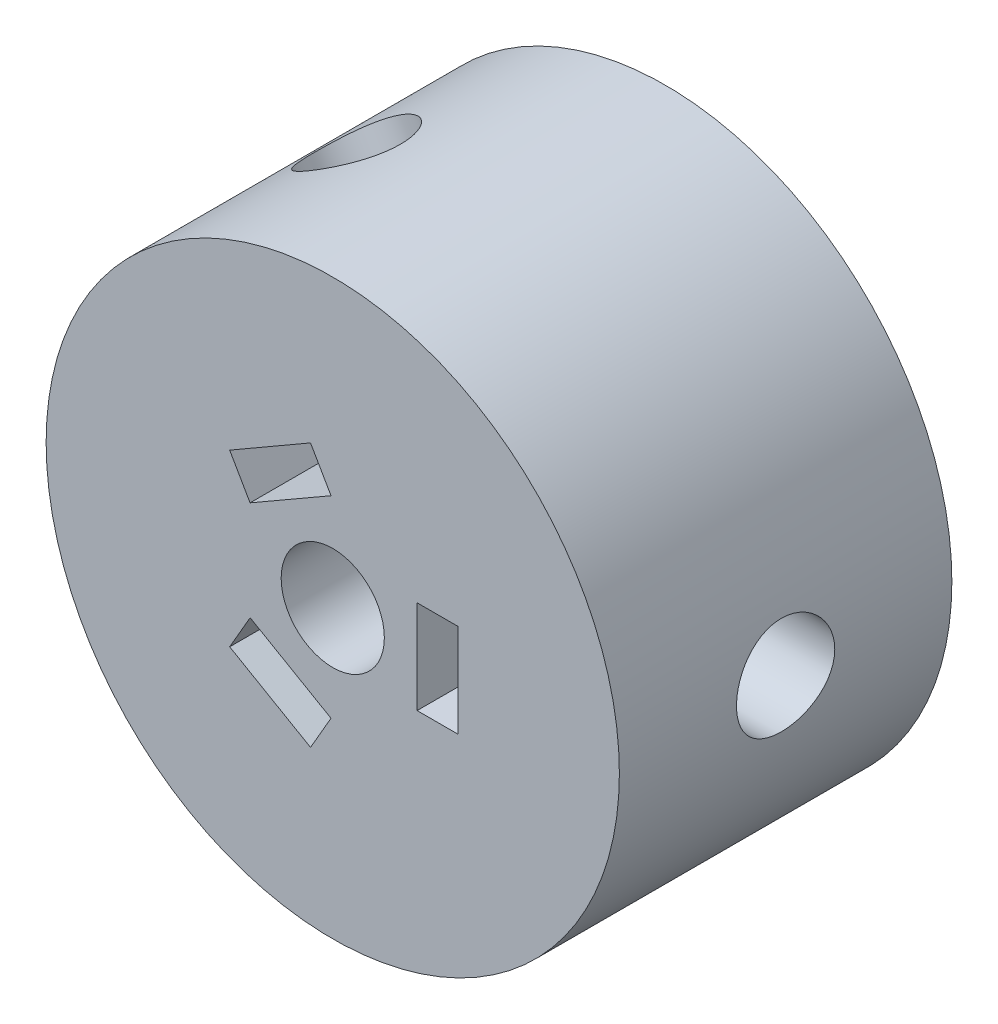
SolidWorks part; units mm, degrees
ref_plane "Front" through (0, 0, 0) normal (0, 0, 1) x (1, 0, 0)
ref_plane "Top" through (0, 0, 0) normal (0, 1, 0) x (1, 0, 0)
ref_plane "Right" through (0, 0, 0) normal (1, 0, 0) x (0, 0, -1)
sketch "Sketch1" plane through (0, 0, 0) normal (0, 0, 1) x (1, 0, 0)
  circle A0 centre (0, 0) radius 17.5
  circle A1 centre (0, 0) radius 3.15
  dimension "D1" = 35
  dimension "D2" = 6.3
extrude "Boss-Extrude1" add sketch "Sketch1" along normal blind 40.3
sketch "Sketch2" plane through (0, 0, 40.3) normal (0, 0, 1) x (1, 0, 0)
  line L3 (7.65, 0) -> (7.65, 2.85)
  line L5 (7.65, 0) -> (7.65, -2.85)
  line L7 (7.65, 2.85) -> (5.15, 2.85)
  line L8 (5.15, 2.85) -> (5.15, -2.85)
  line L9 (5.15, -2.85) -> (7.65, -2.85)
  line L16 (-3.825, -6.6251) -> (-1.3568, -8.0501)
  line L17 (-3.825, -6.6251) -> (-6.2932, -5.2001)
  line L18 (-1.3568, -8.0501) -> (-0.1068, -5.885)
  line L19 (-0.1068, -5.885) -> (-5.0432, -3.035)
  line L20 (-5.0432, -3.035) -> (-6.2932, -5.2001)
  line L21 (-3.825, 6.6251) -> (-6.2932, 5.2001)
  line L22 (-3.825, 6.6251) -> (-1.3568, 8.0501)
  line L23 (-1.3568, 8.0501) -> (-0.1054, 5.8826)
  line L24 (-0.1054, 5.8826) -> (-5.0482, 3.0353)
  line L25 (-5.0482, 3.0353) -> (-6.2932, 5.2001)
  dimension "D5" = 2.85
  dimension "D6" = 2.85
  dimension "D7" = 2.85
  dimension "D8" = 2.85
  dimension "D9" = 2.5
  dimension "D10" = 5.7
  dimension "D11" = 2.85
extrude "Cut-Extrude1" cut sketch "Sketch2" against normal blind 23 contours L9 L5 L3 L7 L8 | L25 L21 L22 L23 L24 | L20 L17 L16 L18 L19
ref_plane "Plane1" through (-8.75, -15.1554, 0) normal (-0.5, -0.866, 0) x (0, 0, -1)
sketch "Sketch8" plane through (-8.75, -15.1554, 0) normal (-0.5, -0.866, 0) x (0, 0, -1)
  circle A0 centre (-20.15, 0) radius 1.65
  dimension "D1" = 3.3
extrude "Cut-Extrude4" cut sketch "Sketch8" against normal up to next
sketch "Sketch10" plane through (-8.75, -15.1554, 0) normal (-0.5, -0.866, 0) x (0, 0, -1)
  circle A0 centre (-20.15, 0) radius 1.65
extrude "Cut-Extrude5" cut sketch "Sketch10" against normal up to next
sketch "Sketch12" plane through (-8.75, -15.1554, 0) normal (-0.5, -0.866, 0) x (0, 0, -1)
  circle A0 centre (-20.15, 0) radius 3
  dimension "D1" = 6
extrude "Cut-Extrude6" cut sketch "Sketch12" against normal blind 5.35
ref_plane "Plane2" through (-8.75, 15.1554, 0) normal (-0.5, 0.866, 0) x (0, 0, -1)
sketch "Sketch15" plane through (-8.75, 15.1554, 0) normal (-0.5, 0.866, 0) x (0, 0, -1)
  circle A0 centre (-20.15, 0) radius 3
extrude "Cut-Extrude8" cut sketch "Sketch15" against normal blind 5.35
sketch "Sketch17" plane through (-8.75, 15.1554, 0) normal (-0.5, 0.866, 0) x (0, 0, -1)
  circle A0 centre (-20.15, 0) radius 1.65
  dimension "D1" = 3.3
extrude "Cut-Extrude9" cut sketch "Sketch17" against normal up to next
sketch "Sketch18" plane through (-8.75, 15.1554, 0) normal (-0.5, 0.866, 0) x (0, 0, -1)
  circle A0 centre (-20.15, 0) radius 1.65
extrude "Cut-Extrude10" cut sketch "Sketch18" against normal up to next
ref_plane "Plane3" through (17.5, 0, 0) normal (1, 0, 0) x (0, 0, -1)
sketch "Sketch19" plane through (17.5, 0, 0) normal (1, 0, 0) x (0, 0, -1)
  circle A0 centre (-20.15, 0) radius 3
extrude "Cut-Extrude11" cut sketch "Sketch19" against normal blind 5.35 contours A0
sketch "Sketch20" plane through (17.5, 0, 0) normal (1, 0, 0) x (0, 0, -1)
  circle A0 centre (-20.15, 0) radius 1.65
  dimension "D1" = 3.3
extrude "Cut-Extrude12" cut sketch "Sketch20" against normal up to next
sketch "Sketch21" plane through (17.5, 0, 0) normal (1, 0, 0) x (0, 0, -1)
  circle A0 centre (-20.15, 0) radius 1.65
extrude "Cut-Extrude13" cut sketch "Sketch21" against normal up to next
sketch "Sketch22" plane through (0, 0, 0) normal (0, 0, -1) x (-1, 0, 0)
  circle A0 centre (0, 0) radius 17.5
extrude "Cut-Extrude14" cut sketch "Sketch22" against normal blind 10
sketch "Sketch23" plane through (0, 0, 40.3) normal (0, 0, 1) x (1, 0, 0)
  circle A0 centre (0, 0) radius 17.5
extrude "Cut-Extrude15" cut sketch "Sketch23" against normal blind 10
